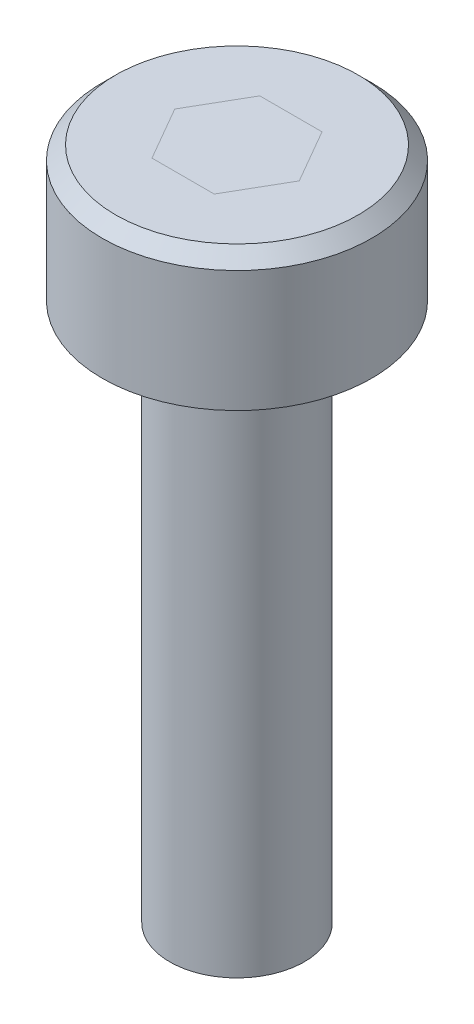
SolidWorks part; units mm, degrees
material "STEEL 1018"
ref_plane "Front Plane" through (0, 0, 0) normal (0, 0, 1) x (1, 0, 0)
ref_plane "Top Plane" through (0, 0, 0) normal (0, 1, 0) x (1, 0, 0)
ref_plane "Right Plane" through (0, 0, 0) normal (1, 0, 0) x (0, 0, -1)
sketch "SK_CBORE" plane through (0, 0, 0) normal (0, 1, 0) x (0, 0, -1)
  circle A0 centre (0, 0) radius 5
  dimension "CBORE_SIZE" = 10
extrude "BD_CBORE" add sketch "SK_CBORE" along normal blind 5
sketch "SK_THREAD" plane through (0, 0, 0) normal (0, -1, 0) x (1, 0, 0)
  circle A0 centre (0, 0) radius 2.5
  dimension "THREAD_SIZE" = 5
extrude "BD_THREAD" add sketch "SK_THREAD" along normal blind 20
cosmetic thread "CT_THREAD" parameters "CT_DEPTH"=10, "CT_SIZE"=4.67
sketch "SK_SOCKET" plane through (0, 5, 0) normal (0, 1, 0) x (1, 0, 0)
  line L1 (-1.1547, 2) -> (-2.3094, 0)
  line L2 (-2.3094, 0) -> (-1.1547, -2)
  line L3 (-1.1547, -2) -> (1.1547, -2)
  line L4 (1.1547, -2) -> (2.3094, 0)
  line L5 (2.3094, 0) -> (1.1547, 2)
  line L6 (1.1547, 2) -> (-1.1547, 2)
  circle A0 centre (0, 0) radius 2 construction
  dimension "SOCKET_SIZE" = 4
split line "SPLIT_SOCKET"
chamfer "CF_CBORE" distance 0.5 angle 45 1 edges at (0, 5, 5)
